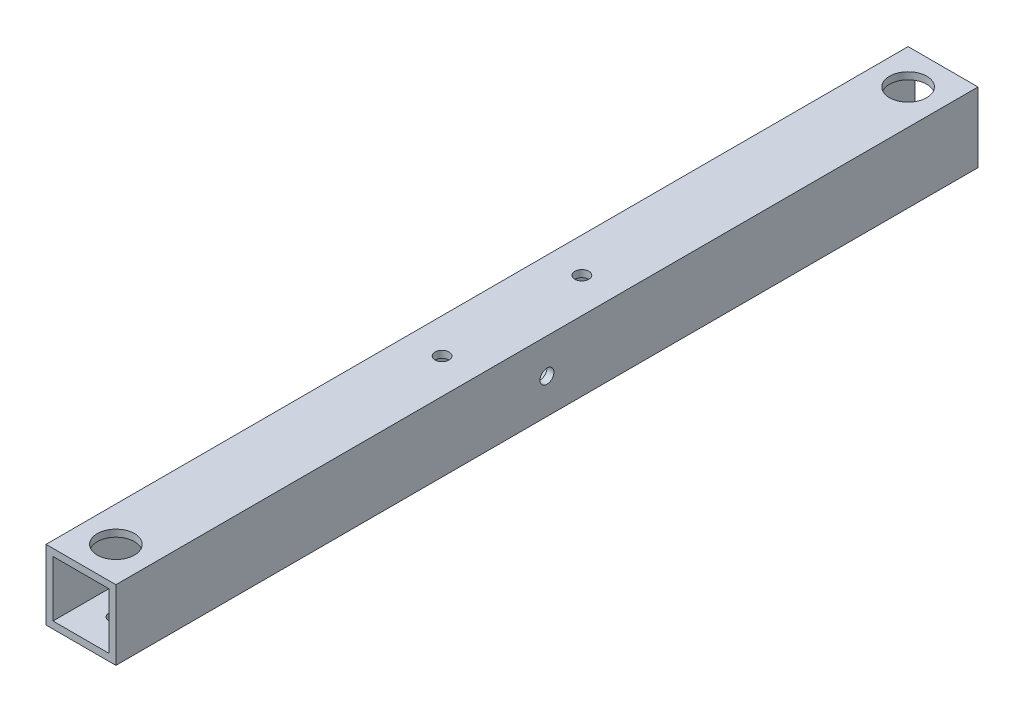
SolidWorks part; units mm, degrees
material "1060 合金"
ref_plane "正面" through (0, 0, 0) normal (0, 0, 1) x (1, 0, 0)
ref_plane "平面" through (0, 0, 0) normal (0, 1, 0) x (1, 0, 0)
ref_plane "右側面" through (0, 0, 0) normal (1, 0, 0) x (0, 0, -1)
sketch "ｽｹｯﾁ1" plane through (0, 0, 0) normal (0, 0, 1) x (1, 0, 0)
  line L1 (-7.0101, 7.7326) -> (7.9899, 7.7326)
  line L2 (-7.0101, 7.7326) -> (-7.0101, -7.2674)
  line L3 (-7.0101, -7.2674) -> (7.9899, -7.2674)
  line L4 (7.9899, 7.7326) -> (7.9899, -7.2674)
  line L9 (-5.5101, 6.2326) -> (6.4899, 6.2326)
  line L10 (-5.5101, 6.2326) -> (-5.5101, -5.7674)
  line L11 (-5.5101, -5.7674) -> (6.4899, -5.7674)
  line L12 (6.4899, 6.2326) -> (6.4899, -5.7674)
  dimension "D1" = 15
  dimension "D2" = 15
  dimension "D3" = 1.5
  dimension "D4" = 1.5
  dimension "D5" = 12
  dimension "D6" = 12
extrude "ﾎﾞｽ - 押し出し2" add sketch "ｽｹｯﾁ1" along normal blind 185
sketch "ｽｹｯﾁ2" plane through (0, 7.7326, 0) normal (0, 1, 0) x (1, 0, 0)
  line L0 (7.9899, 0) -> (-7.0101, 0) construction
  circle A0 centre (0.4899, -7.5) radius 4
  dimension "D1" = 7.5
extrude "ｶｯﾄ - 押し出し1" cut sketch "ｽｹｯﾁ2" against normal blind 10
sketch "ｽｹｯﾁ3" plane through (0, 7.7326, 0) normal (0, 1, 0) x (1, 0, 0)
  line L0 (7.9899, -185) -> (-7.0101, -185) construction
  circle A0 centre (0.4899, -177.5) radius 4
  dimension "D1" = 7.5
extrude "ｶｯﾄ - 押し出し2" cut sketch "ｽｹｯﾁ3" against normal blind 10
sketch "ｽｹｯﾁ4" plane through (0, -7.2674, 0) normal (0, -1, 0) x (1, 0, 0)
  line L0 (-7.0101, 0) -> (7.9899, 0) construction
  circle A0 centre (0.4899, 7.5) radius 1.5
  dimension "D1" = 7.5
extrude "ｶｯﾄ - 押し出し3" cut sketch "ｽｹｯﾁ4" against normal blind 10
sketch "ｽｹｯﾁ5" plane through (0, -7.2674, 0) normal (0, -1, 0) x (1, 0, 0)
  line L0 (-7.0101, 185) -> (7.9899, 185) construction
  line L1 (7.9899, 185) -> (7.9899, 0) construction
  circle A0 centre (0.4899, 177.5) radius 1.5
  dimension "D1" = 7.5
  dimension "D2" = 7.5
extrude "ｶｯﾄ - 押し出し4" cut sketch "ｽｹｯﾁ5" against normal blind 10
sketch "ｽｹｯﾁ6" plane through (0, 7.7326, 0) normal (0, 1, 0) x (1, 0, 0)
  line L3 (-7.0101, -92.5) -> (-7.0101, -77.5)
  line L4 (-7.0101, -185) -> (-7.0101, 0) construction
  circle A1 centre (0.4899, -77.5) radius 1.5
  dimension "D1" = 7.5
  dimension "D2" = 15
extrude "ｶｯﾄ - 押し出し5" cut sketch "ｽｹｯﾁ6" against normal blind 10 contours A1
sketch "ｽｹｯﾁ8" plane through (0, 7.7326, 0) normal (0, 1, 0) x (1, 0, 0)
  line L0 (7.9899, -185) -> (7.9899, 0) construction
  circle A0 centre (0.4899, -107.5) radius 1.5
  circle A1 centre (0.4899, -77.5) radius 1.5 construction
  dimension "D1" = 30
  dimension "D2" = 7.5
extrude "ｶｯﾄ - 押し出し6" cut sketch "ｽｹｯﾁ8" against normal blind 10
sketch "ｽｹｯﾁ9" plane through (0, -7.2674, 0) normal (0, -1, 0) x (1, 0, 0)
  line L0 (7.9899, 185) -> (7.9899, 0) construction
  line L1 (7.9899, 92.5) -> (0.4899, 92.5)
  line L2 (7.9899, 92.5) -> (7.9899, 77.5)
  line L3 (7.9899, 77.5) -> (0.4899, 77.5)
  line L4 (0.4899, 92.5) -> (0.4899, 77.5)
  circle A0 centre (0.4899, 77.5) radius 4
  dimension "D1" = 7.5
  dimension "D2" = 15
extrude "ｶｯﾄ - 押し出し7" cut sketch "ｽｹｯﾁ9" against normal blind 10 contours L4 A0 L3 | L3 A0 L4
sketch "ｽｹｯﾁ10" plane through (0, -7.2674, 0) normal (0, -1, 0) x (1, 0, 0)
  line L0 (-7.0101, 185) -> (-7.0101, 0) construction
  circle A0 centre (0.4899, 107.5) radius 4
  circle A1 centre (0.4899, 77.5) radius 4 construction
  dimension "D1" = 30
  dimension "D2" = 7.5
extrude "ｶｯﾄ - 押し出し8" cut sketch "ｽｹｯﾁ10" against normal blind 10
sketch "ｽｹｯﾁ11" plane through (7.9899, 0, 0) normal (1, 0, 0) x (0, 0, -1)
  line L0 (-185, 7.7326) -> (0, 7.7326) construction
  circle A0 centre (-92.5, 0.2326) radius 1.5
  point P5 (-92.5, 7.7326)
  dimension "D1" = 7.5
extrude "ｶｯﾄ - 押し出し9" cut sketch "ｽｹｯﾁ11" against normal blind 10
sketch "ｽｹｯﾁ12" plane through (-7.0101, 0, 0) normal (-1, 0, 0) x (0, 0, 1)
  line L1 (185, 7.7326) -> (0, 7.7326) construction
  circle A0 centre (92.5, 0.2326) radius 4
  point P3 (92.5, 7.7326)
  dimension "D2" = 7.5
extrude "ｶｯﾄ - 押し出し10" cut sketch "ｽｹｯﾁ12" against normal blind 10
